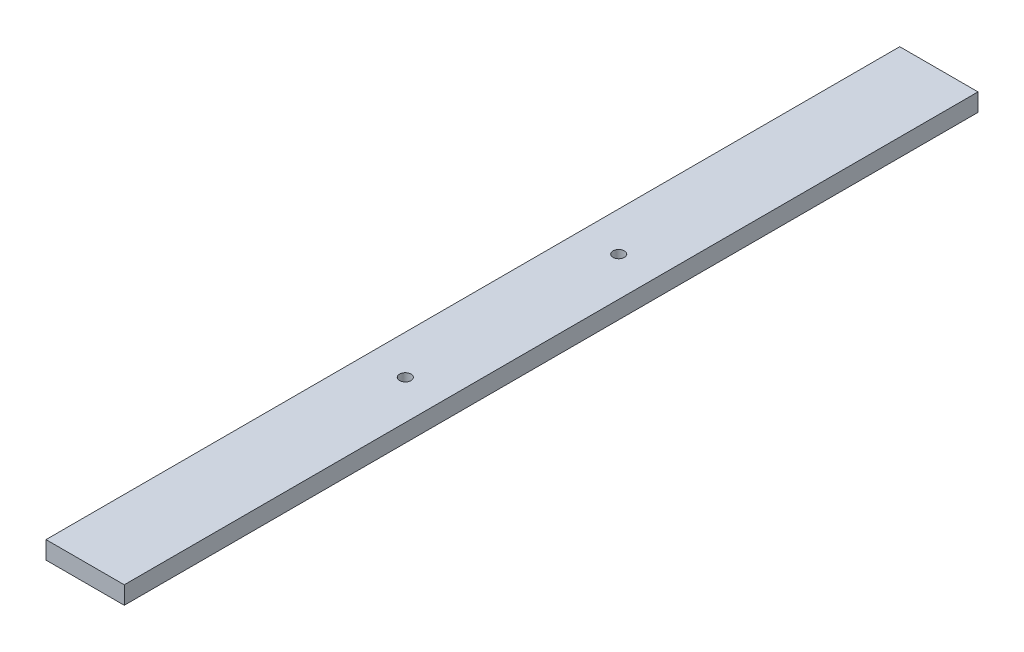
SolidWorks part; units mm, degrees
ref_plane "Front Plane" through (0, 0, 0) normal (0, 0, 1) x (1, 0, 0)
ref_plane "Top Plane" through (0, 0, 0) normal (0, 1, 0) x (1, 0, 0)
ref_plane "Right Plane" through (0, 0, 0) normal (1, 0, 0) x (0, 0, -1)
sketch "Sketch1" plane through (0, 0, 0) normal (0, 0, 1) x (1, 0, 0)
  line L1 (-11, -2.5) -> (11, -2.5)
  line L2 (-11, -2.5) -> (-11, 2.5)
  line L3 (-11, 2.5) -> (11, 2.5)
  line L4 (11, -2.5) -> (11, 2.5)
  line L5 (-11, -2.5) -> (11, 2.5) construction
  line L6 (-11, 2.5) -> (11, -2.5) construction
  point P0 (0, 0)
  dimension "D1" = 22
  dimension "D2" = 5
extrude "Boss-Extrude1" add sketch "Sketch1" against normal blind 240
sketch "Sketch2" plane through (0, 2.5, 0) normal (0, 1, 0) x (1, 0, 0)
  line L0 (0, 240) -> (0, 0) construction
  line L1 (11, 240) -> (-11, 240) construction
  line L2 (11, 0) -> (-11, 0) construction
  line L3 (-11, 120) -> (11, 120) construction
  line L4 (-11, 240) -> (-11, 0) construction
  line L5 (11, 240) -> (11, 0) construction
  circle A0 centre (0, 150) radius 1.6
  circle A1 centre (0, 90) radius 1.6
  dimension "D1" = 3.2
  dimension "D2" = 30
extrude "Cut-Extrude1" cut sketch "Sketch2" against normal through all
